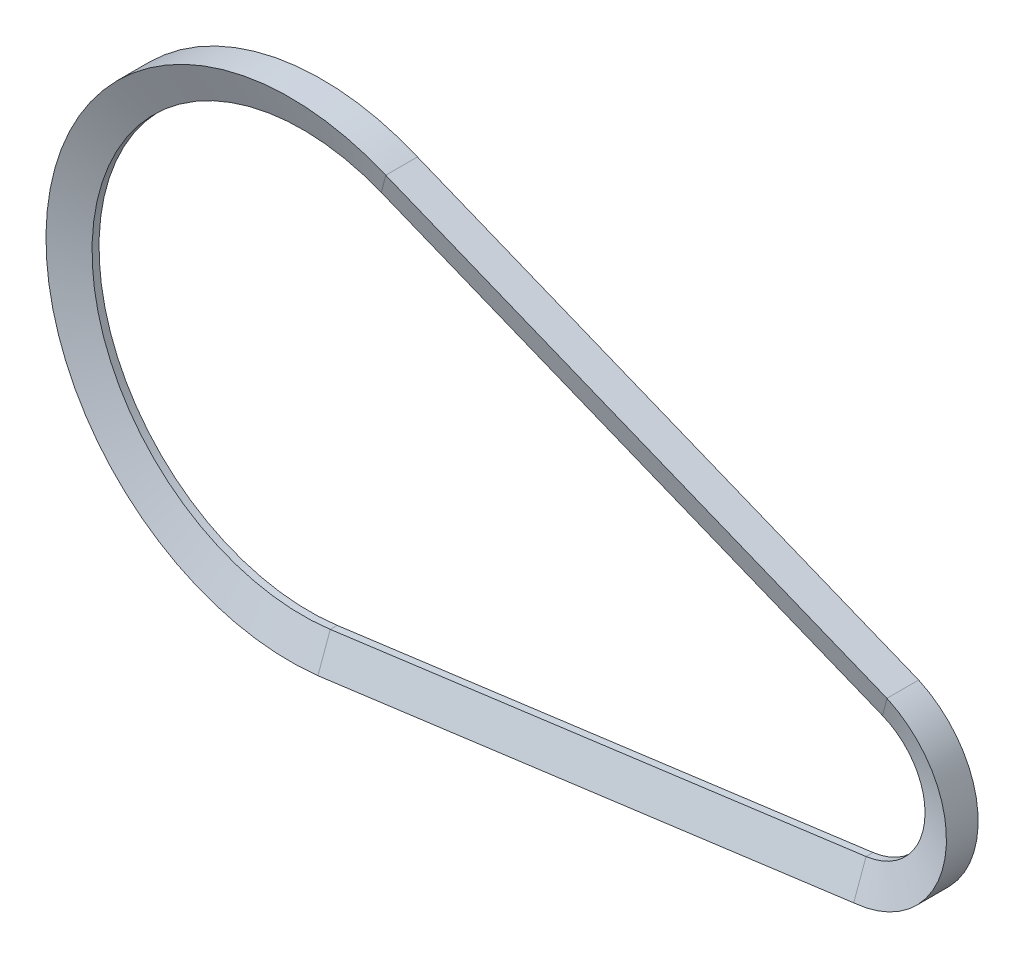
SolidWorks part; units mm, degrees
ref_plane "Front Plane" through (0, 0, 0) normal (0, 0, 1) x (1, 0, 0)
ref_plane "Top Plane" through (0, 0, 0) normal (0, 1, 0) x (1, 0, 0)
ref_plane "Right Plane" through (0, 0, 0) normal (1, 0, 0) x (0, 0, -1)
sketch "Sketch4" plane through (0, 0, 0) normal (0, 0, 1) x (1, 0, 0)
  line L0 (6.1247, -46.0949) -> (124.4757, -30.3693)
  line L1 (17.4127, 43.1167) -> (128.117, -1.5914)
  arc A0 (17.4127, 43.1167) -> (6.1247, -46.0949) centre (0, 0) ccw
  arc A1 (124.4757, -30.3693) -> (128.117, -1.5914) centre (122.5, -15.5) ccw
  dimension "D3" = 93
  dimension "D4" = 30
  dimension "D1" = 15.5
  dimension "D2" = 122.5
ref_plane "Plane1" through (6.1247, 0, 0) normal (1, 0, 0) x (0, 0, -1)
sketch "Sketch5" plane through (6.1247, 0, 0) normal (1, 0, 0) x (0, 0, -1)
  line L0 (0, -46.0949) -> (0, 3.2756) construction
  line L1 (-0.7702, -46.0949) -> (0.7702, -46.0949)
  line L5 (0.7702, -46.0949) -> (3.5, -53.5949)
  line L6 (3.5, -53.5949) -> (-3.5, -53.5949)
  line L7 (-3.5, -53.5949) -> (-0.7702, -46.0949)
  line L8 (0, -46.0949) -> (0, -53.5949) construction
  dimension "D1" = 7.5
  dimension "D2" = 40
sweep "Sweep1" add profiles "Sketch5" path "Sketch4"
